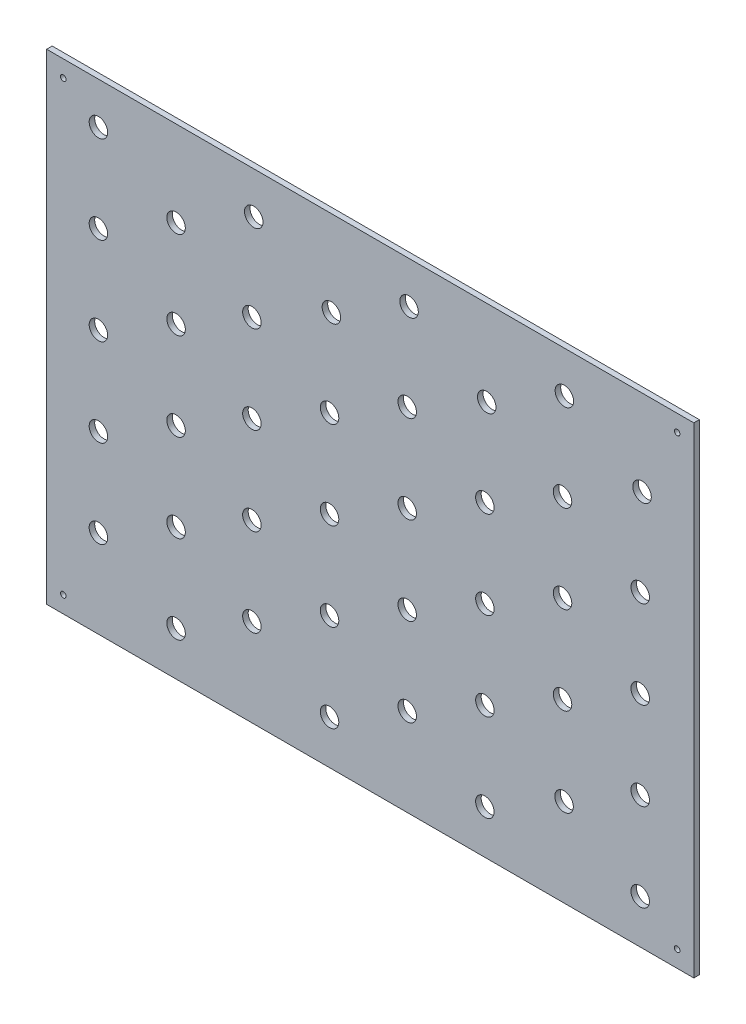
SolidWorks part; units mm, degrees
material "ABS PC"
ref_plane "Alzado" through (0, 0, 0) normal (0, 0, 1) x (1, 0, 0)
ref_plane "Planta" through (0, 0, 0) normal (0, 1, 0) x (1, 0, 0)
ref_plane "Vista lateral" through (0, 0, 0) normal (1, 0, 0) x (0, 0, -1)
sketch "Croquis2" plane through (0, 0, 0) normal (0, 0, 1) x (1, 0, 0)
  line L2 (-73.0327, 40.4815) -> (276.9673, 40.4815)
  line L3 (-73.0327, 40.4815) -> (-73.0327, -219.5185)
  line L4 (-73.0327, -219.5185) -> (276.9673, -219.5185)
  line L8 (276.9673, 40.4815) -> (276.9673, -219.5185)
  circle A0 centre (-45.0327, 17.9815) radius 5
  circle A1 centre (-45.0327, -29.5185) radius 5
  circle A2 centre (-45.0327, -77.0185) radius 5
  circle A3 centre (-45.0327, -124.5185) radius 5
  circle A4 centre (-45.0327, -172.0185) radius 5
  circle A5 centre (-3.0327, -5.7685) radius 5
  circle A6 centre (38.9673, 17.9815) radius 5
  circle A7 centre (80.9673, -5.7685) radius 5
  circle A8 centre (122.9673, 17.9815) radius 5
  circle A9 centre (164.9673, -5.7685) radius 5
  circle A10 centre (-3.0327, -53.2685) radius 5
  circle A11 centre (-3.0327, -100.7685) radius 5
  circle A12 centre (-3.0327, -148.2685) radius 5
  circle A13 centre (-3.0327, -195.7685) radius 5
  circle A14 centre (37.9673, -29.5185) radius 5
  circle A15 centre (37.9673, -77.0185) radius 5
  circle A16 centre (37.9673, -124.5185) radius 5
  circle A17 centre (37.9673, -172.0185) radius 5
  circle A18 centre (79.9673, -53.2685) radius 5
  circle A19 centre (79.9673, -100.7685) radius 5
  circle A20 centre (79.9673, -148.2685) radius 5
  circle A21 centre (79.9673, -195.7685) radius 5
  circle A22 centre (121.9673, -29.5185) radius 5
  circle A23 centre (163.9673, -53.2685) radius 5
  circle A24 centre (121.9673, -77.0185) radius 5
  circle A25 centre (163.9673, -100.7685) radius 5
  circle A26 centre (121.9673, -124.5185) radius 5
  circle A27 centre (121.9673, -172.0185) radius 5
  circle A28 centre (163.9673, -148.2685) radius 5
  circle A29 centre (163.9673, -195.7685) radius 5
  circle A30 centre (206.9673, 18.0715) radius 5
  circle A31 centre (205.9673, -29.5185) radius 5
  circle A32 centre (205.9673, -77.0185) radius 5
  circle A33 centre (205.9673, -124.5185) radius 5
  circle A34 centre (206.7962, -171.9285) radius 5
  circle A35 centre (248.9673, -5.7685) radius 5
  circle A36 centre (247.9673, -53.2685) radius 5
  circle A37 centre (247.9673, -100.7685) radius 5
  circle A38 centre (247.9673, -148.2685) radius 5
  circle A39 centre (247.9673, -195.7685) radius 5
  circle A40 centre (-64.0327, -210.5185) radius 1.5
  circle A41 centre (267.9673, -210.5185) radius 1.5
  circle A42 centre (267.9673, 31.4815) radius 1.5
  circle A43 centre (-64.0327, 31.4815) radius 1.5
  point P78 (265.8224, -208.4983)
  dimension "D3" = 10
  dimension "D4" = 9
  dimension "D24" = 9
  dimension "D5" = 9
  dimension "D6" = 47.5
  dimension "D7" = 47.5
  dimension "D8" = 47.5
  dimension "D9" = 47.5
  dimension "D10" = 9
  dimension "D11" = 42
  dimension "D12" = 42
  dimension "D13" = 42
  dimension "D14" = 42
  dimension "D15" = 42
  dimension "D16" = 47.5
  dimension "D17" = 47.5
  dimension "D18" = 47.5
  dimension "D19" = 47.5
  dimension "D20" = 42
  dimension "D21" = 42
  dimension "D22" = 9
  dimension "D23" = 9
  dimension "D25" = 9
  dimension "D26" = 9
  dimension "D27" = 350
  dimension "D28" = 260
extrude "Saliente-Extruir1" add sketch "Croquis2" along normal blind 3
